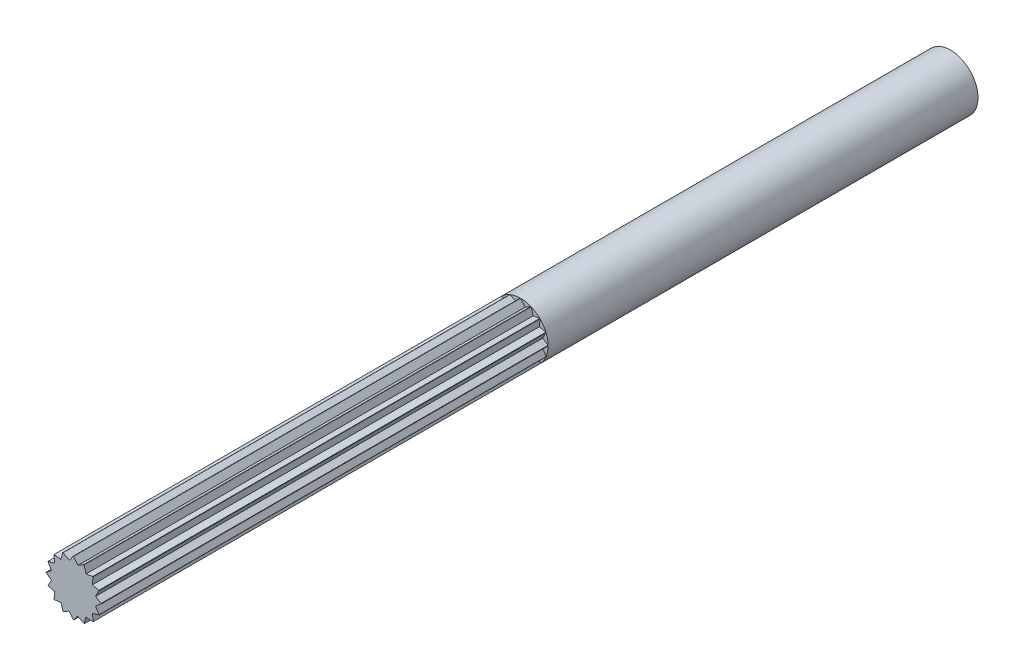
SolidWorks part; units mm, degrees
material "AISI Type 316L stainless steel"
ref_plane "Front Plane" through (0, 0, 0) normal (0, 0, 1) x (1, 0, 0)
ref_plane "Top Plane" through (0, 0, 0) normal (0, 1, 0) x (1, 0, 0)
ref_plane "Right Plane" through (0, 0, 0) normal (1, 0, 0) x (0, 0, -1)
sketch "Sketch1" plane through (0, 0, 0) normal (0, 0, 1) x (1, 0, 0)
  circle A0 centre (0, 0) radius 1.6
extrude "Extrude1" add sketch "Sketch1" along normal blind 51
sketch "Sketch2" plane through (0, 0, 51) normal (0, 0, 1) x (1, 0, 0)
  line L0 (0, 1.6) -> (1.6, 0) construction
  line L1 (1.6, 0) -> (0, -1.6) construction
  line L2 (0, -1.6) -> (-1.6, 0) construction
  line L3 (-1.6, 0) -> (0, 1.6) construction
  line L4 (0, 0) -> (1.1314, 1.1314) construction
  line L5 (0, 0) -> (1.1314, -1.1314) construction
  line L6 (0, 0) -> (-1.1314, 1.1314) construction
  line L7 (0, 0) -> (-1.1314, -1.1314) construction
  line L8 (-1.1314, 1.1314) -> (-1.1314, -1.1314) construction
  line L9 (-1.1314, -1.1314) -> (1.1314, -1.1314) construction
  line L10 (1.1314, -1.1314) -> (1.1314, 1.1314) construction
  line L11 (1.1314, 1.1314) -> (-1.1314, 1.1314) construction
  line L12 (0, 0) -> (0.4686, 1.1314) construction
  line L13 (0, 0) -> (1.1314, 0.4686) construction
  line L14 (0, 0) -> (1.1314, -0.4686) construction
  line L15 (0, 0) -> (0.4686, -1.1314) construction
  line L16 (1.2864, 0.2331) -> (1.5997, 0.0296)
  line L21 (1.2864, 0.2331) -> (1.4717, 0.6096)
  line L22 (1.5997, 0.0296) -> (1.8731, 0.4503)
  line L23 (1.8731, 0.4503) -> (1.4717, 0.6096)
  line L24 (1.6, 0) -> (1.2814, -0.2596)
  line L25 (1.2814, -0.2596) -> (1.4853, -0.595)
  line L26 (1.4853, -0.595) -> (1.786, -0.4)
  line L27 (1.786, -0.4) -> (1.6, 0)
  line L28 (1.4782, -0.6123) -> (1.095, -0.7143)
  line L29 (1.095, -0.7143) -> (1.15, -1.1124)
  line L30 (1.15, -1.1124) -> (1.5606, -1.0557)
  line L31 (1.5606, -1.0557) -> (1.4782, -0.6123)
  line L32 (1.1314, -1.1314) -> (0.7207, -1.0908)
  line L33 (0.7207, -1.0908) -> (0.6292, -1.4711)
  line L34 (0.6292, -1.4711) -> (1.0339, -1.5685)
  line L35 (1.0339, -1.5685) -> (1.1314, -1.1314)
  line L36 (0.6123, -1.4782) -> (0.2387, -1.2854)
  line L37 (0.3347, -1.7924) -> (0.0093, -1.6)
  line L38 (0.0093, -1.6) -> (0.2387, -1.2854)
  line L39 (0.3347, -1.7924) -> (0.6123, -1.4782)
  line L40 (0, -1.6) -> (-0.2544, -1.2824)
  line L41 (-0.2544, -1.2824) -> (-0.6005, -1.483)
  line L42 (-0.6005, -1.483) -> (-0.4123, -1.8075)
  line L43 (-0.4123, -1.8075) -> (0, -1.6)
  line L44 (-0.6123, -1.4782) -> (-0.7207, -1.0908)
  line L45 (-0.7207, -1.0908) -> (-1.1216, -1.141)
  line L46 (-1.1216, -1.141) -> (-1.0759, -1.5061)
  line L47 (-1.0759, -1.5061) -> (-0.6123, -1.4782)
  line L48 (-1.1314, -1.1314) -> (-1.087, -0.7265)
  line L49 (-1.087, -0.7265) -> (-1.4743, -0.6216)
  line L50 (-1.4743, -0.6216) -> (-1.5685, -0.9694)
  line L51 (-1.5685, -0.9694) -> (-1.1314, -1.1314)
  line L52 (-1.4782, -0.6123) -> (-1.2854, -0.2387)
  line L53 (-1.2854, -0.2387) -> (-1.6, -0.0093)
  line L54 (-1.6, -0.0093) -> (-1.8647, -0.3892)
  line L55 (-1.8647, -0.3892) -> (-1.4782, -0.6123)
  line L56 (-1.6, 0) -> (-1.2854, 0.2387)
  line L57 (-1.2854, 0.2387) -> (-1.4829, 0.6008)
  line L58 (-1.4829, 0.6008) -> (-1.9042, 0.3711)
  line L59 (-1.9042, 0.3711) -> (-1.6, 0)
  line L60 (-1.4782, 0.6123) -> (-1.0993, 0.7076)
  line L61 (-1.0993, 0.7076) -> (-1.1388, 1.1239)
  line L62 (-1.1388, 1.1239) -> (-1.5037, 1.0894)
  line L63 (-1.5037, 1.0894) -> (-1.4782, 0.6123)
  line L64 (-1.1314, 1.1314) -> (-0.7325, 1.0829)
  line L65 (-0.7325, 1.0829) -> (-0.6271, 1.472)
  line L66 (-0.6271, 1.472) -> (-1.1526, 1.4323)
  line L67 (-1.1526, 1.4323) -> (-1.1314, 1.1314)
  line L68 (-0.6123, 1.4782) -> (-0.2387, 1.2854)
  line L69 (-0.2387, 1.2854) -> (-0.0196, 1.5999)
  line L70 (-0.0196, 1.5999) -> (-0.5072, 1.6591)
  line L71 (-0.5072, 1.6591) -> (-0.6123, 1.4782)
  line L72 (0, 1.6) -> (0.2616, 1.281)
  line L73 (0.2616, 1.281) -> (0.5988, 1.4837)
  line L74 (0.5988, 1.4837) -> (0.4301, 1.6013)
  line L75 (0.4301, 1.6013) -> (0.2385, 1.7348)
  line L76 (0.2385, 1.7348) -> (0, 1.6)
  line L77 (0.6123, 1.4782) -> (0.7325, 1.0829)
  line L78 (0.7325, 1.0829) -> (1.1173, 1.1452)
  line L79 (1.1173, 1.1452) -> (1.0565, 1.5213)
  line L80 (1.0565, 1.5213) -> (0.6123, 1.4782)
  line L81 (1.1314, 1.1314) -> (1.095, 0.7143)
  line L82 (1.095, 0.7143) -> (1.4717, 0.6277)
  line L83 (1.4717, 0.6277) -> (1.55, 0.9926)
  line L84 (1.55, 0.9926) -> (1.1314, 1.1314)
  circle A0 centre (0, 0) radius 1.6 construction
  circle A1 centre (0, 0) radius 1.3074 construction
extrude "Extrude8" cut sketch "Sketch2" against normal blind 26
